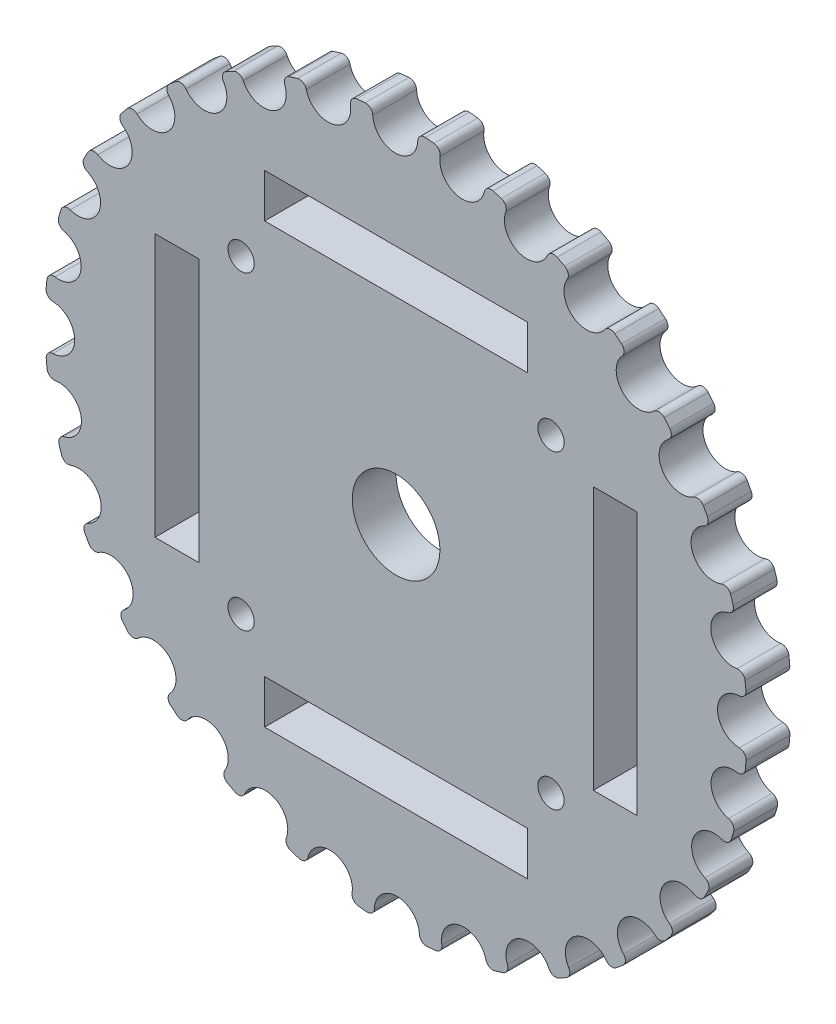
SolidWorks part; units mm, degrees
material "PMMA"
ref_plane "Front Plane" through (0, 0, 0) normal (0, 0, 1) x (1, 0, 0)
ref_plane "Top Plane" through (0, 0, 0) normal (0, 1, 0) x (1, 0, 0)
ref_plane "Right Plane" through (0, 0, 0) normal (1, 0, 0) x (0, 0, -1)
sketch "Schizzo1" plane through (0, 0, 0) normal (0, 0, 1) x (1, 0, 0)
  circle A0 centre (0, 0) radius 40.7437 construction
  circle A1 centre (0, 0) radius 40.0627
  circle A3 centre (0, 0) radius 36.6117 construction
  dimension "D1" = 81.4873
  dimension "D2" = 80.1253
  dimension "D4" = 73.2233
  dimension "D3" = 0.681
extrude "Estrusione-Estrusione1" add sketch "Schizzo1" along normal blind 5
sketch "Schizzo2" plane through (0, 0, 0) normal (0, 0, 1) x (1, 0, 0)
  line L0 (0.0019, 0) -> (-0.0935, 39.2349) construction
  line L1 (0.0019, 0) -> (7.5627, 38.4996) construction
  circle A0 centre (0, 0) radius 40.7437 construction
  circle A1 centre (0, 0) radius 36.665 construction
  circle A2 centre (-0.0935, 39.2349) radius 2.57
  circle A3 centre (7.5627, 38.4996) radius 2.57
  circle A4 centre (14.9283, 36.2848) radius 2.57
  circle A5 centre (21.7203, 32.6756) radius 2.57
  circle A6 centre (27.6777, 27.8107) radius 2.57
  circle A7 centre (32.5715, 21.8771) radius 2.57
  circle A8 centre (36.2137, 15.1027) radius 2.57
  circle A9 centre (38.4643, 7.7479) radius 2.57
  circle A10 centre (39.2368, 0.0954) radius 2.57
  circle A11 centre (38.5015, -7.5608) radius 2.57
  circle A12 centre (36.2867, -14.9264) radius 2.57
  circle A13 centre (32.6775, -21.7184) radius 2.57
  circle A14 centre (27.8126, -27.6758) radius 2.57
  circle A15 centre (21.8789, -32.5696) radius 2.57
  circle A16 centre (15.1046, -36.2118) radius 2.57
  circle A17 centre (7.7498, -38.4624) radius 2.57
  circle A18 centre (0.0973, -39.2349) radius 2.57
  circle A19 centre (-7.5589, -38.4996) radius 2.57
  circle A20 centre (-14.9245, -36.2848) radius 2.57
  circle A21 centre (-21.7165, -32.6756) radius 2.57
  circle A22 centre (-27.6739, -27.8107) radius 2.57
  circle A23 centre (-32.5677, -21.8771) radius 2.57
  circle A24 centre (-36.2099, -15.1027) radius 2.57
  circle A25 centre (-38.4605, -7.7479) radius 2.57
  circle A26 centre (-39.233, -0.0954) radius 2.57
  circle A27 centre (-38.4977, 7.5608) radius 2.57
  circle A28 centre (-36.2829, 14.9264) radius 2.57
  circle A29 centre (-32.6737, 21.7184) radius 2.57
  circle A30 centre (-27.8088, 27.6758) radius 2.57
  circle A31 centre (-21.8752, 32.5696) radius 2.57
  circle A32 centre (-15.1008, 36.2118) radius 2.57
  circle A33 centre (-7.746, 38.4624) radius 2.57
  point P70 (0.0019, 0)
  dimension "D1" = 81.4873
  dimension "D7" = 5.14
  dimension "D2" = 73.33
  dimension "D6" = 7.6914
  dimension "D5" = 11.25
  dimension "D3" = 32
extrude "Taglio-Estrusione1" cut sketch "Schizzo2" along direction (0, 0, 1) on the side of the normal through all
fillet "Raccordo1" radius 0.8 64 edges at (-5.4856, 39.6853, 2.5) (-10.3036, 38.715, 2.5) (-13.1227, 37.8525, 2.5) (-17.6585, 35.961, 2.5) (-20.2554, 34.5649, 2.5) (-24.3349, 31.825, 2.5) (-26.6098, 29.9489, 2.5) (-30.0762, 26.4658, 2.5) (-31.9414, 24.1819, 2.5) (-34.6616, 20.0895, 2.5) (-36.0455, 17.4854, 2.5) (-37.915, 12.9411, 2.5) (-38.7642, 10.1169, 2.5) (-39.7112, 5.2953, 2.5) (-39.9931, 2.3596, 2.5) (-39.9812, -2.5541, 2.5) (-39.6849, -5.4883, 2.5) (-38.7146, -10.3053, 2.5) (-37.8516, -13.1253, 2.5) (-35.96, -17.6605, 2.5) (-34.5635, -20.2579, 2.5) (-31.8234, -24.3369, 2.5) (-29.9471, -26.6118, 2.5) (-26.4638, -30.078, 2.5) (-24.1799, -31.9429, 2.5) (-20.0871, -34.663, 2.5) (-17.4834, -36.0464, 2.5) (-12.9384, -37.9159, 2.5) (-10.1152, -38.7647, 2.5) (-5.2926, -39.7115, 2.5) (-2.3583, -39.9932, 2.5) (2.5566, -39.981, 2.5) (5.4891, -39.6848, 2.5) (10.3075, -38.714, 2.5) (13.1256, -37.8515, 2.5) (17.6621, -35.9592, 2.5) (20.2576, -34.5637, 2.5) (24.338, -31.8226, 2.5) (26.6112, -29.9477, 2.5) (30.0785, -26.4632, 2.5) (31.9421, -24.181, 2.5) (34.6632, -20.0868, 2.5) (36.0457, -17.4851, 2.5) (37.9158, -12.9387, 2.5) (38.7641, -10.1173, 2.5) (39.7114, -5.2934, 2.5) (39.993, -2.3608, 2.5) (39.9811, 2.5553, 2.5) (39.6852, 5.4865, 2.5) (38.7145, 10.3057, 2.5) (37.8524, 13.1229, 2.5) (35.9602, 17.6601, 2.5) (34.5651, 20.2552, 2.5) (31.8241, 24.336, 2.5) (29.9495, 26.6091, 2.5) (26.4652, 30.0767, 2.5) (24.1829, 31.9406, 2.5) (20.0893, 34.6618, 2.5) (17.487, 36.0447, 2.5) (12.9414, 37.9149, 2.5) (10.1191, 38.7637, 2.5) (5.2961, 39.7111, 2.5) (2.3621, 39.993, 2.5) (-2.5528, 39.9812, 2.5)
sketch "Schizzo3" plane through (0, 0, 0) normal (0, 0, 1) x (1, 0, 0)
  circle A0 centre (0, 0) radius 5
  dimension "D1" = 10
extrude "Taglio-Estrusione2" cut sketch "Schizzo3" along direction (0, 0, 1) on the side of the normal through all
sketch "Schizzo4" plane through (0, 0, 0) normal (0, 0, 1) x (1, 0, 0)
  line L0 (0, 0) -> (71.629, 0) construction
  line L2 (15, 27.5) -> (15, 22.5)
  line L3 (-27.5, 15) -> (-22.5, 15)
  line L4 (-27.5, 15) -> (-27.5, -15)
  line L5 (-27.5, -15) -> (-22.5, -15)
  line L6 (-22.5, 15) -> (-22.5, -15)
  line L7 (15, 27.5) -> (-15, 27.5)
  line L8 (-15, 27.5) -> (-15, 22.5)
  line L9 (15, 22.5) -> (-15, 22.5)
  line L10 (27.5, -15) -> (22.5, -15)
  line L11 (27.5, -15) -> (27.5, 15)
  line L12 (27.5, 15) -> (22.5, 15)
  line L13 (22.5, -15) -> (22.5, 15)
  line L14 (-15, -27.5) -> (-15, -22.5)
  line L15 (-15, -27.5) -> (15, -27.5)
  line L16 (15, -27.5) -> (15, -22.5)
  line L17 (-15, -22.5) -> (15, -22.5)
  line L18 (0, 0) -> (-22.5, 15) construction
  line L19 (0, -28.2745) -> (0, 29.7867) construction
  line L20 (-17.677, 17.6783) -> (17.6736, 17.6783) construction
  line L21 (17.6736, 17.6783) -> (17.6736, -17.6817) construction
  line L22 (17.6736, -17.6817) -> (-17.677, -17.6817) construction
  line L23 (-17.677, -17.6817) -> (-17.677, 17.6783) construction
  circle A9 centre (17.6736, 17.6783) radius 1.5
  circle A11 centre (17.6736, -17.6817) radius 1.5
  circle A13 centre (-17.677, -17.6817) radius 1.5
  circle A15 centre (-17.677, 17.6783) radius 1.5
  point P8 (-22.5, 0)
  dimension "D1" = 5
  dimension "D8" = 3
  dimension "D2" = 30
  dimension "D4" = 25
  dimension "D6" = 25
  dimension "D3" = 22.5
  dimension "D7" = 24.9976
  dimension "D9" = 35.36
  dimension "D5" = 4
extrude "Taglio-Estrusione3" cut sketch "Schizzo4" along direction (0, 0, 1) on the side of the normal through all
equation "\"PD\"= ( \"Pitch\" * \"N\" ) / 3.141593'Pitch Diameter"
equation "\"D1@Schizzo1\"=\"PD\""
equation "\"Pitch\"= 8"
equation "\"N\"= 32'Number of Teeth"
equation "\"OD\"= \"PD\" - 2 * \"U\"'Outer Diameter"
equation "\"h_t\"= 3.451mm'Height of the tooth"
equation "\"D2@Schizzo1\"=\"OD\""
equation "\"D3@Schizzo1\"=\"h_t\""
equation "\"U\"= 0.681'distance between the tensile cord and the bottom of the belt tooth"
equation "\"Thickness5\"=5"
equation "\"D1@Estrusione-Estrusione1\"=\"Thickness5\""
equation "\"D1@Schizzo2\"=\"PD\""
equation "\"D_t\"=5.14"
equation "\"D7@Schizzo2\"=\"D_t\""
equation "\"R\"=0.15"
equation "\"D1@Raccordo1\"=\"R_t\""
equation "\"R_t\"=0.8"
equation "\"ID\"= \"OD\" - 2 * \"h_t\""
equation "\"D4@Schizzo1\"=\"ID\""
equation "\"D1@Schizzo4\"=\"Thickness5\""
